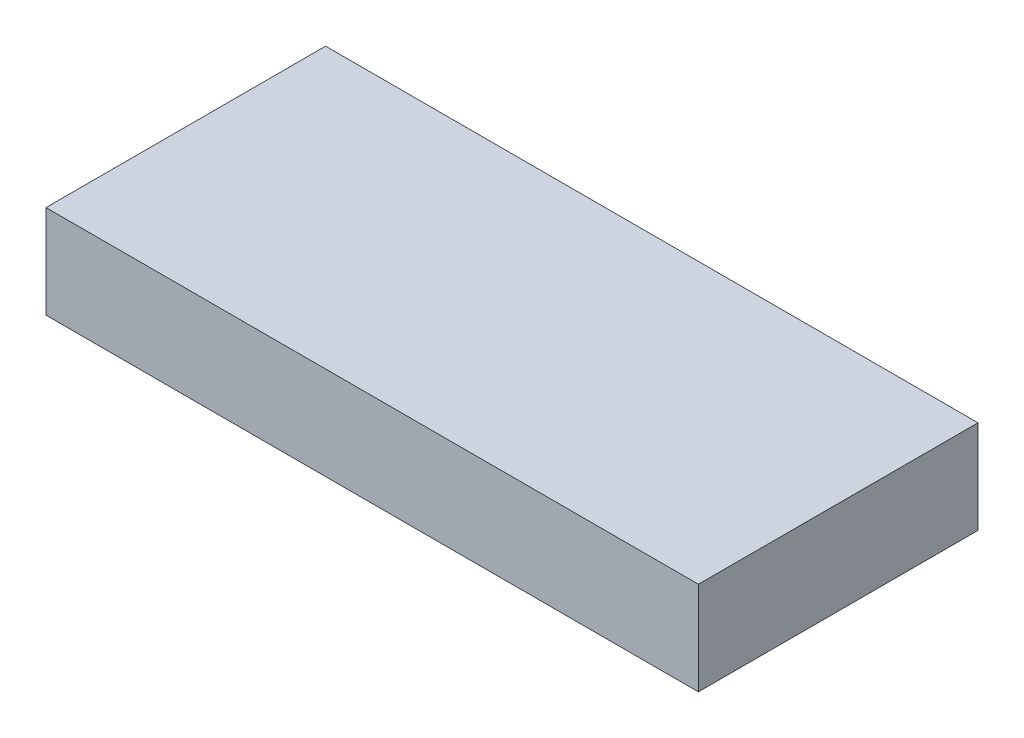
SolidWorks part; units mm, degrees
ref_plane "Front Plane" through (0, 0, 0) normal (0, 0, 1) x (1, 0, 0)
ref_plane "Top Plane" through (0, 0, 0) normal (0, 1, 0) x (1, 0, 0)
ref_plane "Right Plane" through (0, 0, 0) normal (1, 0, 0) x (0, 0, -1)
sketch "Sketch2" plane through (0, 0, 0) normal (0, 1, 0) x (1, 0, 0)
  line L1 (-17.5, 7.5) -> (17.5, 7.5)
  line L2 (-17.5, 7.5) -> (-17.5, -7.5)
  line L3 (-17.5, -7.5) -> (17.5, -7.5)
  line L4 (17.5, 7.5) -> (17.5, -7.5)
  line L5 (-17.5, 7.5) -> (17.5, -7.5) construction
  line L6 (-17.5, -7.5) -> (17.5, 7.5) construction
  point P0 (0, 0)
  dimension "D1" = 15
  dimension "D2" = 35
extrude "Boss-Extrude1" add sketch "Sketch2" along normal blind 5
